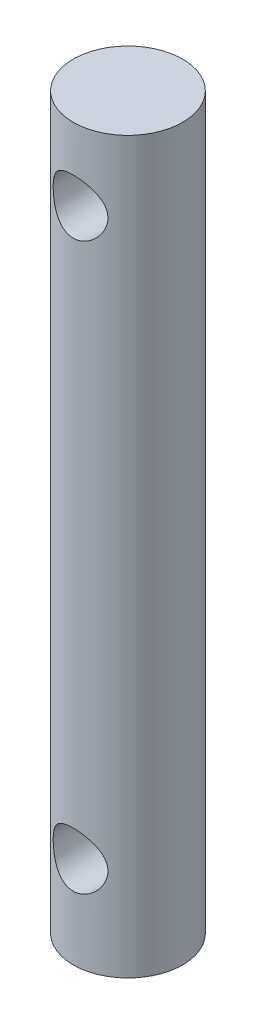
SolidWorks part; units mm, degrees
ref_plane "前基準面" through (0, 0, 0) normal (0, 0, 1) x (1, 0, 0)
ref_plane "上基準面" through (0, 0, 0) normal (0, 1, 0) x (1, 0, 0)
ref_plane "右基準面" through (0, 0, 0) normal (1, 0, 0) x (0, 0, -1)
sketch "草圖1" plane through (0, 0, 0) normal (0, 1, 0) x (1, 0, 0)
  circle A1 centre (0, 0) radius 3
  dimension "D1" = 6
extrude "填料-伸長1" add sketch "草圖1" along normal mid plane 40
sketch "草圖2" plane through (0, 0, 0) normal (0, 0, 1) x (1, 0, 0)
  line L0 (-9.0203, 0) -> (10.9835, 0) construction
  line L1 (3, 20) -> (-3, 20) construction
  line L2 (-3, -20) -> (3, -20) construction
  circle A0 centre (0, 16) radius 1.5
  circle A1 centre (0, -15) radius 1.5
  point P5 (0, 0)
  dimension "D1" = 3
  dimension "D2" = 4
  dimension "D3" = 5
extrude "除料-伸長1" cut sketch "草圖2" against normal through all both and the other way through all
